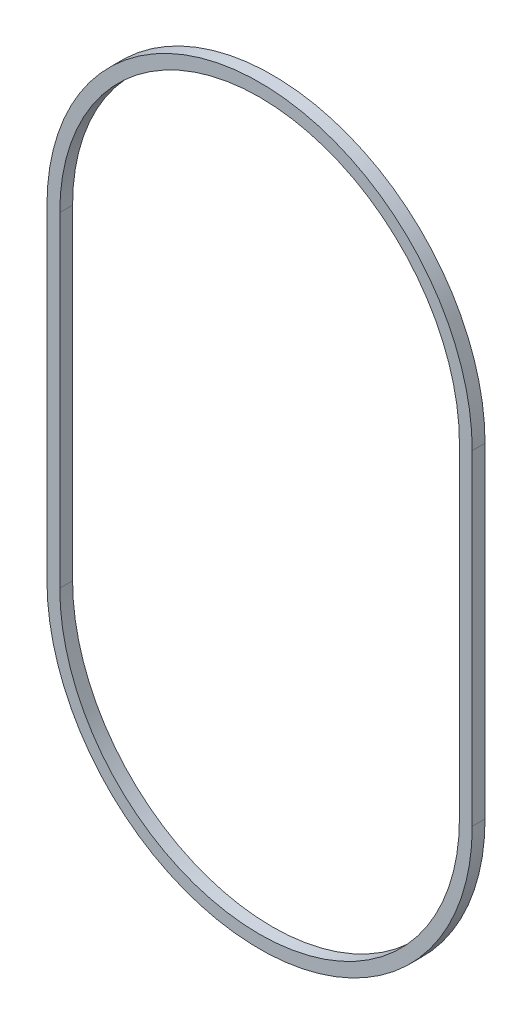
SolidWorks part; units mm, degrees
ref_plane "Front Plane" through (0, 0, 0) normal (0, 0, 1) x (1, 0, 0)
ref_plane "Top Plane" through (0, 0, 0) normal (0, 1, 0) x (1, 0, 0)
ref_plane "Right Plane" through (0, 0, 0) normal (1, 0, 0) x (0, 0, -1)
sketch "Sketch1" plane through (0, 0, 0) normal (0, 0, 1) x (1, 0, 0)
  line L0 (0, 31.75) -> (0, -31.75) construction
  line L1 (39, 31.75) -> (39, -31.75)
  line L2 (-39, 31.75) -> (-39, -31.75)
  line L3 (41.5, 31.75) -> (41.5, -31.75)
  line L4 (-41.5, 31.75) -> (-41.5, -31.75)
  arc A0 (39, 31.75) -> (-39, 31.75) centre (0, 31.75) ccw
  arc A1 (-39, -31.75) -> (39, -31.75) centre (0, -31.75) ccw
  arc A2 (-41.5, -31.75) -> (41.5, -31.75) centre (0, -31.75) ccw
  arc A3 (41.5, 31.75) -> (-41.5, 31.75) centre (0, 31.75) ccw
  point P2 (0, 0)
  dimension "D1" = 63.5
  dimension "D2" = 78
  dimension "D3" = 2.5
extrude "Boss-Extrude1" add sketch "Sketch1" along normal blind 2.5
